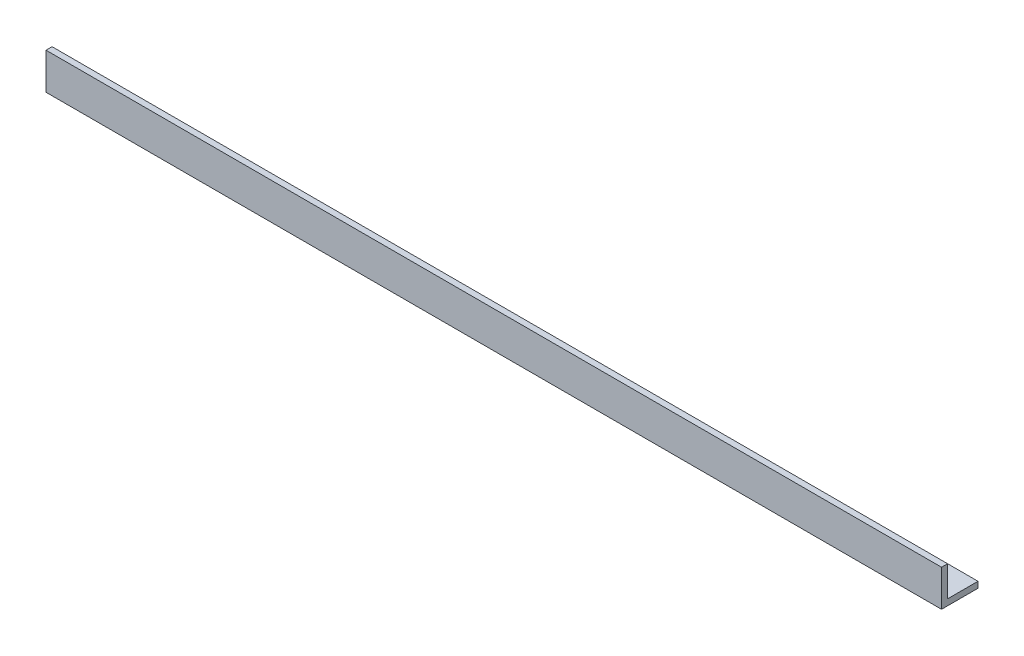
SolidWorks part; units mm, degrees
ref_plane "Front Plane" through (0, 0, 0) normal (0, 0, 1) x (1, 0, 0)
ref_plane "Top Plane" through (0, 0, 0) normal (0, 1, 0) x (1, 0, 0)
ref_plane "Right Plane" through (0, 0, 0) normal (1, 0, 0) x (0, 0, -1)
sketch "Sketch1" plane through (0, 0, 0) normal (1, 0, 0) x (0, 0, -1)
  line L0 (0, 0) -> (0, 19.05)
  line L1 (0, 19.05) -> (3.175, 19.05)
  line L2 (3.175, 19.05) -> (3.175, 3.175)
  line L3 (3.175, 3.175) -> (19.05, 3.175)
  line L4 (19.05, 3.175) -> (19.05, 0)
  line L5 (19.05, 0) -> (0, 0)
extrude "Boss-Extrude1" add sketch "Sketch1" against normal blind 468
sketch "Sketch2" plane through (0, 3.175, 0) normal (0, 1, 0) x (1, 0, 0)
  circle A0 centre (-20.45, 11.2735) radius 2.3813
  circle A1 centre (-56.2, 11.2735) radius 2.3812
  circle A2 centre (-91.95, 11.2735) radius 2.3813
  circle A3 centre (-127.7, 11.2735) radius 2.3813
  circle A4 centre (-163.45, 11.2735) radius 2.3813
  circle A5 centre (-199.2, 11.2735) radius 2.3813
  circle A6 centre (-234.95, 11.2735) radius 2.3813
  circle A7 centre (-270.7, 11.2735) radius 2.3813
  circle A8 centre (-306.45, 11.2735) radius 2.3813
  circle A9 centre (-342.2, 11.2735) radius 2.3813
  circle A10 centre (-377.95, 11.2735) radius 2.3813
  circle A11 centre (-413.7, 11.2735) radius 2.3813
  circle A12 centre (-449.45, 11.2735) radius 2.3813
extrude "Cut-Extrude1" cut sketch "Sketch2" against normal blind 3.175
